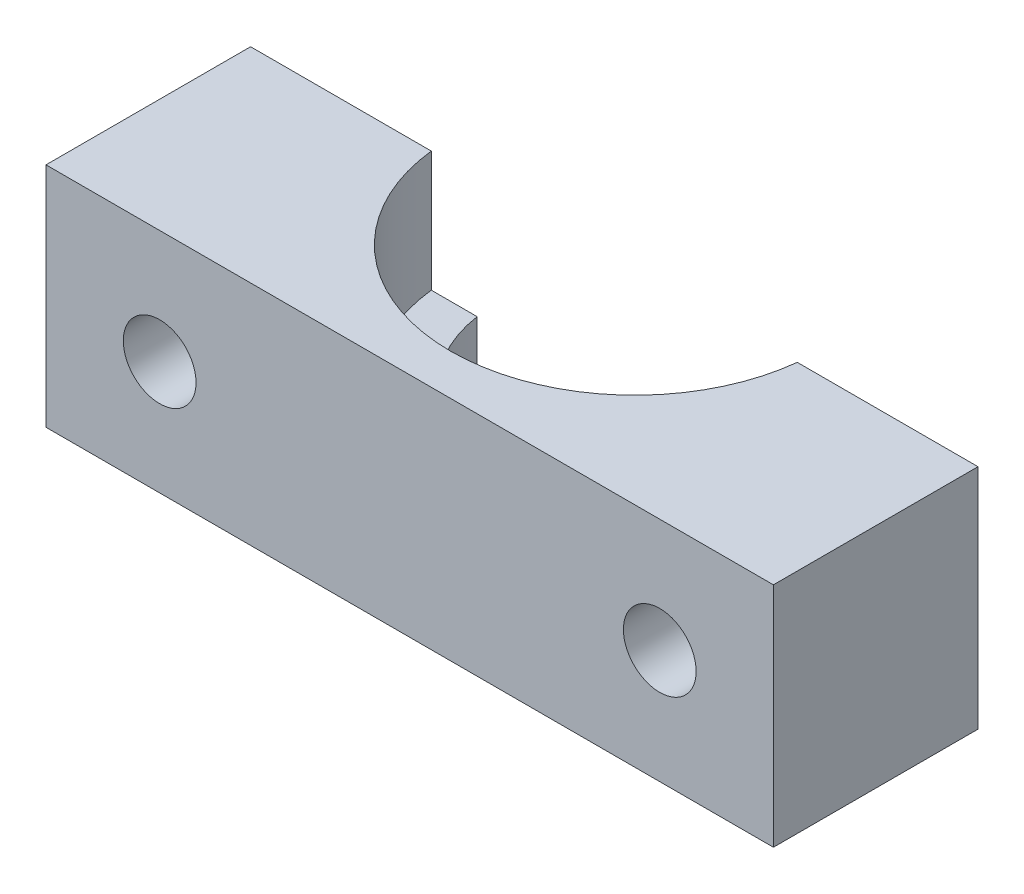
SolidWorks part; units mm, degrees
ref_plane "Front Plane" through (0, 0, 0) normal (0, 0, 1) x (1, 0, 0)
ref_plane "Top Plane" through (0, 0, 0) normal (0, 1, 0) x (1, 0, 0)
ref_plane "Right Plane" through (0, 0, 0) normal (1, 0, 0) x (0, 0, -1)
sketch "Sketch1" plane through (0, 0, 0) normal (0, 0, 1) x (1, 0, 0)
  line L1 (0, 0) -> (32, 0)
  line L2 (0, 0) -> (0, -27)
  line L3 (0, -27) -> (32, -27)
  line L4 (32, 0) -> (32, -27)
  circle A0 centre (8.5, -3.5) radius 1.5
  circle A1 centre (23.5, -3.5) radius 1.5
  circle A2 centre (8.5, -23.5) radius 1.5
  circle A3 centre (23.5, -23.5) radius 1.5
  dimension "D3" = 3
  dimension "D4" = 3
  dimension "D5" = 3
  dimension "D6" = 3
  dimension "D1" = 27
  dimension "D2" = 32
  dimension "D7" = 3.5
  dimension "D8" = 3.5
  dimension "D9" = 3.5
  dimension "D10" = 3.5
  dimension "D11" = 8.5
  dimension "D12" = 8.5
  dimension "D13" = 8.5
  dimension "D14" = 8.5
extrude "Boss-Extrude1" add sketch "Sketch1" along normal blind 25
sketch "Sketch3" plane through (0, 0, 0) normal (-1, 0, 0) x (0, 0, 1)
  line L1 (25, 0) -> (5, 0)
  line L2 (25, 0) -> (25, -10)
  line L3 (25, -10) -> (5, -10)
  line L4 (5, 0) -> (5, -10)
  line L5 (25, -27) -> (5, -27)
  line L6 (25, -27) -> (25, -20)
  line L7 (25, -20) -> (5, -20)
  line L8 (5, -27) -> (5, -20)
  dimension "D1" = 10
  dimension "D2" = 20
  dimension "D3" = 7
  dimension "D4" = 20
extrude "Cut-Extrude1" cut sketch "Sketch3" against normal through all
sketch "Sketch4" plane through (0, -10, 0) normal (0, 1, 0) x (1, 0, 0)
  line L6 (32, -5) -> (0, -5) construction
  line L7 (0, -5) -> (0, -25) construction
  circle A0 centre (15.9997, -15.1) radius 6.1
  point P6 (0, -15)
  dimension "D1" = 12.2
  dimension "D2" = 4
  dimension "D3" = 16
extrude "Cut-Extrude6" cut sketch "Sketch4" against normal through all
sketch "Sketch5" plane through (0, -10, 0) normal (0, 1, 0) x (1, 0, 0)
  circle A0 centre (15.9997, -15.1) radius 8.1
  dimension "D1" = 16.2
extrude "Cut-Extrude7" cut sketch "Sketch5" against normal blind 5.3
sketch "Sketch7" plane through (0, 0, 25) normal (0, 0, 1) x (1, 0, 0)
  line L0 (32, -10) -> (0, -10) construction
  line L1 (32, -10) -> (0, -10) construction
  line L2 (0, -10) -> (0, -20) construction
  line L3 (32, -20) -> (32, -10) construction
  circle A0 centre (5, -15) radius 1.6
  circle A1 centre (27, -15) radius 1.6
  dimension "D1" = 3.2
  dimension "D2" = 3.2
  dimension "D3" = 5
  dimension "D4" = 5
  dimension "D5" = 5
  dimension "D6" = 5
extrude "Cut-Extrude8" cut sketch "Sketch7" against normal through all
sketch "Sketch9" plane through (0, 0, 0) normal (0, 0, -1) x (-1, 0, 0)
  line L1 (-29.1388, -12.8256) -> (-29.9525, -15.765)
  line L2 (-29.9525, -15.765) -> (-27.8137, -17.9394)
  line L3 (-27.8137, -17.9394) -> (-24.8612, -17.1744)
  line L4 (-24.8612, -17.1744) -> (-24.0475, -14.235)
  line L5 (-24.0475, -14.235) -> (-26.1863, -12.0606)
  line L6 (-26.1863, -12.0606) -> (-29.1388, -12.8256)
  line L7 (-5, -11.95) -> (-7.6414, -13.475)
  line L8 (-7.6414, -13.475) -> (-7.6414, -16.525)
  line L9 (-7.6414, -16.525) -> (-5, -18.05)
  line L10 (-5, -18.05) -> (-2.3586, -16.525)
  line L11 (-2.3586, -16.525) -> (-2.3586, -13.475)
  line L12 (-2.3586, -13.475) -> (-5, -11.95)
  circle A0 centre (-27, -15) radius 2.6414 construction
  circle A1 centre (-5, -15) radius 2.6414 construction
  dimension "D1" = 6.1
  dimension "D2" = 6.1
extrude "Cut-Extrude9" cut sketch "Sketch9" against normal blind 10
sketch "Sketch10" plane through (0, 0, 0) normal (0, 0, -1) x (-1, 0, 0)
  line L1 (0, -27) -> (-32, -27)
  line L2 (0, -27) -> (0, 0)
  line L3 (0, 0) -> (-32, 0)
  line L4 (-32, -27) -> (-32, 0)
extrude "Cut-Extrude10" cut sketch "Sketch10" against normal blind 16
